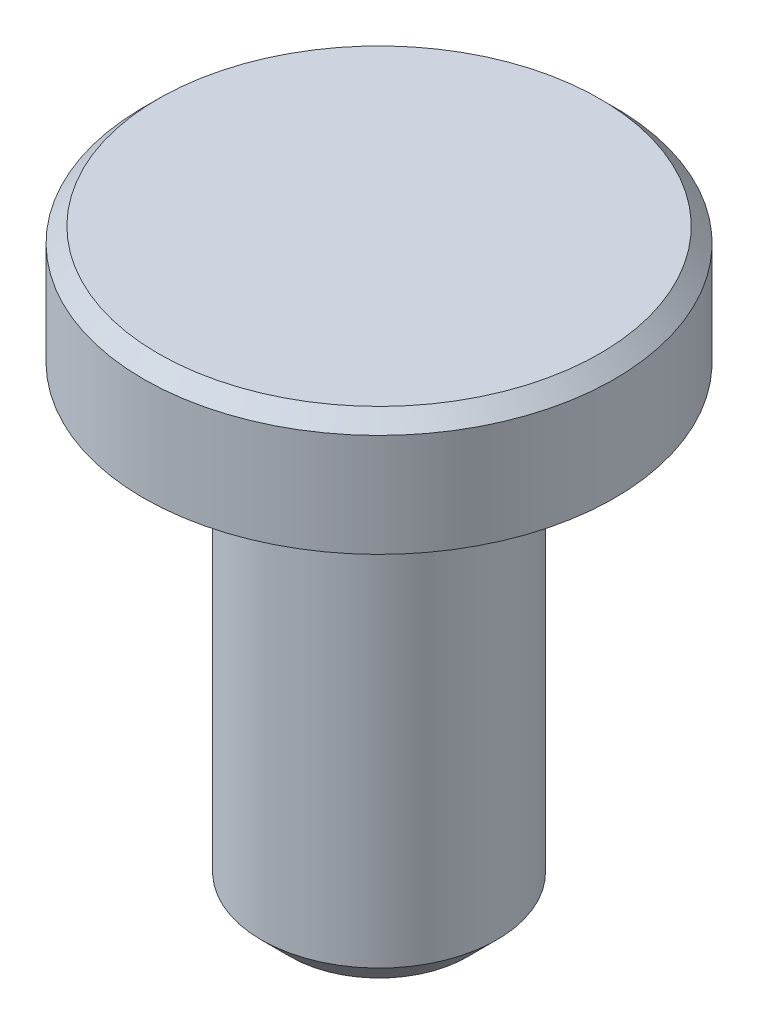
SolidWorks part; units mm, degrees
ref_plane "Front Plane" through (0, 0, 0) normal (0, 0, 1) x (1, 0, 0)
ref_plane "Top Plane" through (0, 0, 0) normal (0, 1, 0) x (1, 0, 0)
ref_plane "Right Plane" through (0, 0, 0) normal (1, 0, 0) x (0, 0, -1)
sketch "Sketch1" plane through (0, 0, 0) normal (0, 1, 0) x (1, 0, 0)
  circle A0 centre (0, 0) radius 8
  circle A1 centre (0, 0) radius 4
  dimension "D1" = 8
  dimension "D2" = 16
extrude "Boss-Extrude1" add sketch "Sketch1" against normal blind 16 contours A1
sketch "Sketch2" plane through (0, 0, 0) normal (0, 1, 0) x (1, 0, 0)
  circle A0 centre (0, 0) radius 8
  dimension "D1" = 16
extrude "Boss-Extrude2" add sketch "Sketch2" along normal blind 4
chamfer "Chamfer1" distance 1 angle 45 1 edges at (0, -16, 4)
chamfer "Chamfer2" distance 0.5 angle 45 1 edges at (0, 4, 8)
fillet "Fillet1" radius 0.3 1 edges at (0, 0, 4)
